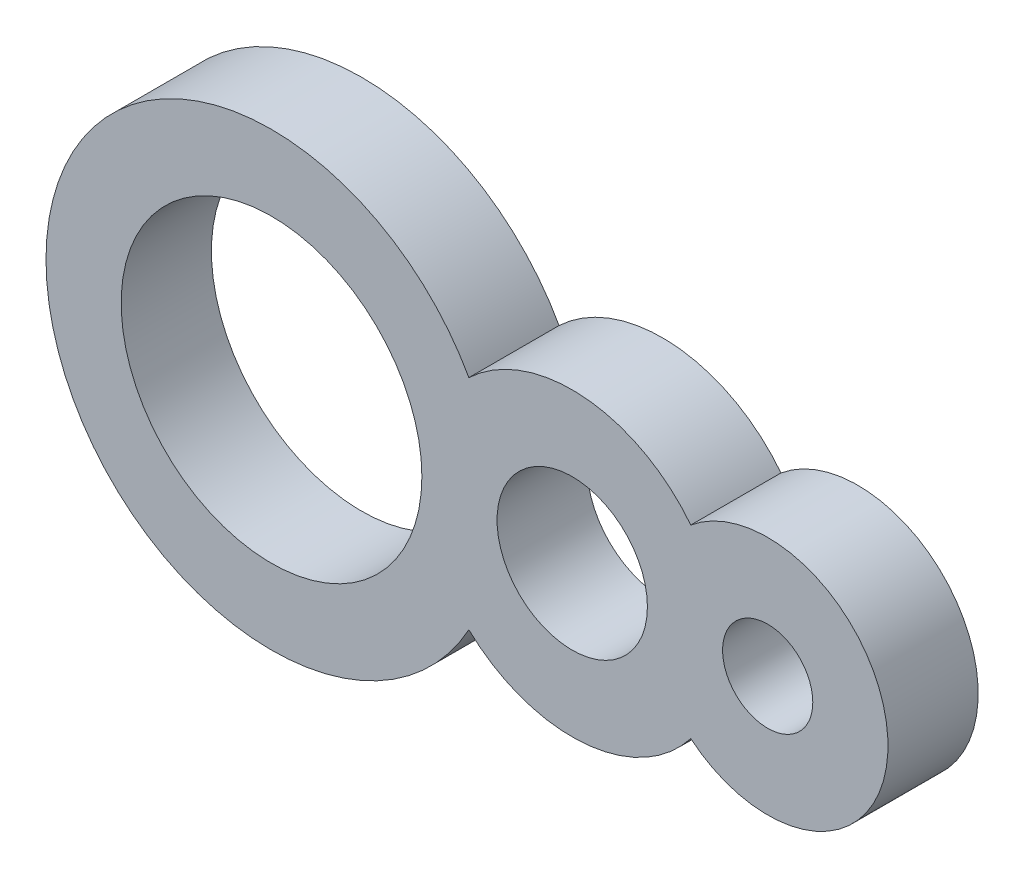
SolidWorks part; units mm, degrees
ref_plane "Front Plane" through (0, 0, 0) normal (0, 0, 1) x (1, 0, 0)
ref_plane "Top Plane" through (0, 0, 0) normal (0, 1, 0) x (1, 0, 0)
ref_plane "Right Plane" through (0, 0, 0) normal (1, 0, 0) x (0, 0, -1)
sketch "Sketch1" plane through (0, 0, 0) normal (0, 0, 1) x (1, 0, 0)
  arc A0 (6.5625, 3.6309) -> (6.5625, -3.6309) centre (0, 0) ccw
  circle A1 centre (0, 0) radius 5
  arc A2 (6.5625, -3.6309) -> (13.9423, -3.0754) centre (10, 0) ccw
  circle A3 centre (10, 0) radius 2.5
  arc A4 (13.9423, -3.0754) -> (13.9423, 3.0754) centre (16.5, 0) ccw
  circle A5 centre (16.5, 0) radius 1.5
  arc A6 (13.9423, 3.0754) -> (6.5625, 3.6309) centre (10, 0) ccw
  point P10 (0, 0)
  dimension "D1" = 15
  dimension "D2" = 10
  dimension "D3" = 5
  dimension "D4" = 10
  dimension "D5" = 3
  dimension "D6" = 8
extrude "Boss-Extrude1" add sketch "Sketch1" along normal blind 3
